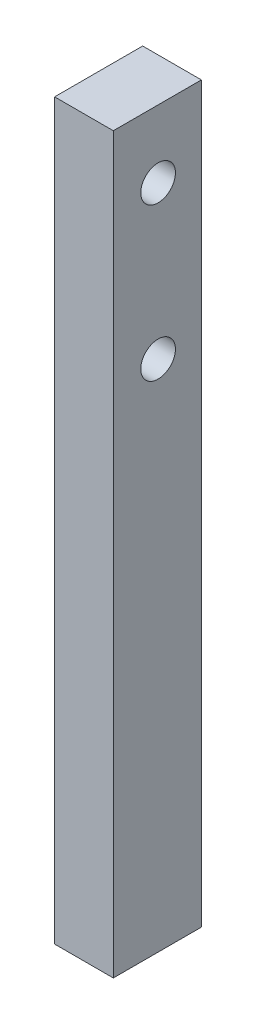
SolidWorks part; units mm, degrees
ref_plane "Front Plane" through (0, 0, 0) normal (0, 0, 1) x (1, 0, 0)
ref_plane "Top Plane" through (0, 0, 0) normal (0, 1, 0) x (1, 0, 0)
ref_plane "Right Plane" through (0, 0, 0) normal (1, 0, 0) x (0, 0, -1)
sketch "Sketch1" plane through (0, 0, 0) normal (0, 0, 1) x (1, 0, 0)
  line L1 (0, 0) -> (5.08, 0)
  line L2 (0, 0) -> (0, 63.5)
  line L3 (0, 63.5) -> (5.08, 63.5)
  line L4 (5.08, 0) -> (5.08, 63.5)
  dimension "D1" = 5.08
  dimension "D2" = 63.5
extrude "Boss-Extrude1" add sketch "Sketch1" along normal blind 7.62
sketch "Sketch2" plane through (0, 0, 0) normal (-1, 0, 0) x (0, 0, 1)
  line L0 (7.62, 0) -> (0, 0) construction
  circle A0 centre (3.7445, 57.658) radius 1.5
  circle A1 centre (3.7445, 44.45) radius 1.5
  dimension "D1" = 3
  dimension "D2" = 3
  dimension "D3" = 13.208
  dimension "D4" = 44.45
extrude "Cut-Extrude1" cut sketch "Sketch2" against normal through all
